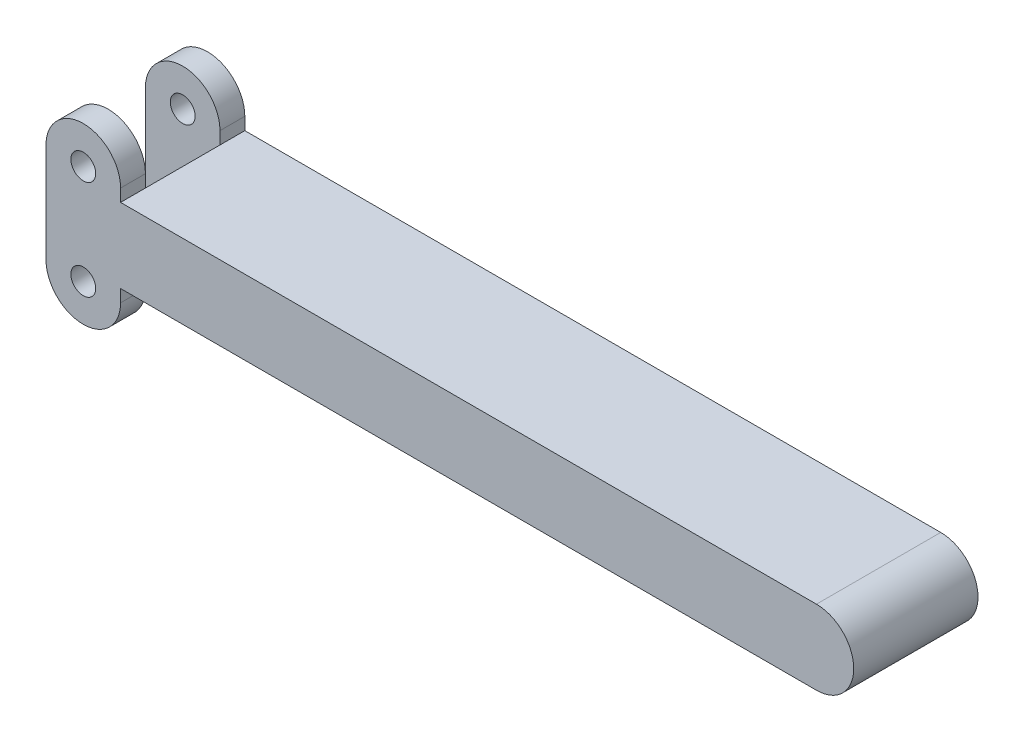
SolidWorks part; units mm, degrees
ref_plane "Front Plane" through (0, 0, 0) normal (0, 0, 1) x (1, 0, 0)
ref_plane "Top Plane" through (0, 0, 0) normal (0, 1, 0) x (1, 0, 0)
ref_plane "Right Plane" through (0, 0, 0) normal (1, 0, 0) x (0, 0, -1)
sketch "Sketch1" plane through (0, 0, 0) normal (0, 0, 1) x (1, 0, 0)
  line L0 (0, 0) -> (0, 25.4) construction
  line L1 (-9.525, 0) -> (-9.525, 25.4)
  line L2 (9.525, 0) -> (9.525, 25.4)
  line L3 (9.525, 22.225) -> (187.325, 22.225)
  line L4 (9.525, 3.175) -> (187.325, 3.175)
  line L5 (0, 12.7) -> (9.525, 22.225) construction
  line L6 (0, 12.7) -> (9.525, 3.175) construction
  arc A0 (-9.525, 0) -> (9.525, 0) centre (0, 0) ccw
  arc A1 (9.525, 25.4) -> (-9.525, 25.4) centre (0, 25.4) ccw
  arc A2 (187.325, 22.225) -> (187.325, 3.175) centre (187.325, 12.7) cw
  circle A3 centre (0, 25.4) radius 3.175
  circle A4 centre (0, 0) radius 3.175
  point P3 (0, 12.7)
  point P17 (9.525, 12.7)
  dimension "D1" = 9.525
  dimension "D5" = 6.35
  dimension "D2" = 25.4
  dimension "D3" = 19.05
  dimension "D6" = 177.8
extrude "Boss-Extrude1" add sketch "Sketch1" along normal blind 31.75
sketch "Sketch2" plane through (-9.525, 0, 0) normal (-1, 0, 0) x (0, 0, 1)
  line L0 (0, 0) -> (0, -9.525) construction
  line L1 (0, 0) -> (31.75, 0) construction
  line L2 (31.75, -9.525) -> (31.75, 0) construction
  line L3 (0, 34.925) -> (0, 25.4) construction
  line L4 (31.75, 25.4) -> (31.75, 34.925) construction
  line L5 (31.75, 25.4) -> (0, 25.4) construction
  line L6 (0, 25.4) -> (0, 0) construction
  line L7 (31.75, 0) -> (31.75, 25.4) construction
  line L8 (0, 0) -> (0, -9.525)
  line L9 (0, 0) -> (31.75, 0)
  line L10 (31.75, -9.525) -> (31.75, 0)
  line L11 (0, 34.925) -> (0, 25.4)
  line L12 (31.75, 25.4) -> (31.75, 34.925)
  line L13 (31.75, 25.4) -> (0, 25.4)
  line L14 (0, 25.4) -> (0, 0)
  line L15 (31.75, 0) -> (31.75, 25.4)
  line L16 (31.75, 34.925) -> (0, 34.925) construction
  line L17 (6.35, 34.925) -> (25.4, 34.925)
  line L18 (6.35, 34.925) -> (6.35, -9.525)
  line L19 (6.35, -9.525) -> (25.4, -9.525)
  line L20 (25.4, 34.925) -> (25.4, -9.525)
  line L21 (0, -9.525) -> (31.75, -9.525) construction
  dimension "D1" = 19.05
  dimension "D2" = 6.35
extrude "Cut-Extrude1" cut sketch "Sketch2" against normal blind 19.05 contours L20 L13 L18 L9 | L20 L17 L18 L13 | L20 L9 L18 L19
